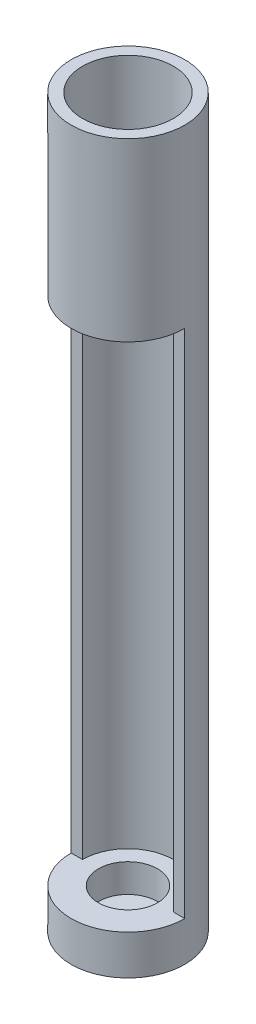
SolidWorks part; units mm, degrees
material "ABS PC"
ref_plane "Front Plane" through (0, 0, 0) normal (0, 0, 1) x (1, 0, 0)
ref_plane "Top Plane" through (0, 0, 0) normal (0, 1, 0) x (1, 0, 0)
ref_plane "Right Plane" through (0, 0, 0) normal (1, 0, 0) x (0, 0, -1)
sketch "Sketch1" plane through (0, 0, 0) normal (0, 1, 0) x (1, 0, 0)
  circle A0 centre (0, 0) radius 5
  dimension "D1" = 10
extrude "Boss-Extrude1" add sketch "Sketch1" along normal blind 3.5
sketch "Sketch2" plane through (0, 3.5, 0) normal (0, 1, 0) x (1, 0, 0)
  circle A0 centre (0, 0) radius 2.6
  dimension "D1" = 5.2
extrude "Cut-Extrude1" cut sketch "Sketch2" against normal blind 2.5
sketch "Sketch3" plane through (0, 3.5, 0) normal (0, 1, 0) x (1, 0, 0)
  line L0 (5, 0) -> (4, 0)
  line L1 (-5, 0) -> (-4, 0)
  arc A0 (5, 0) -> (-5, 0) centre (0, 0) ccw
  circle A1 centre (0, 0) radius 5 construction
  arc A2 (4, 0) -> (-4, 0) centre (0, 0) ccw
  circle M4 centre (0, 0) radius 5
  dimension "D1" = 1
  dimension "D2" = 1
extrude "Boss-Extrude2" add sketch "Sketch3" along normal blind 45 contours A2 L0 L1 M4
sketch "Sketch4" plane through (0, 48.5, 0) normal (0, 1, 0) x (1, 0, 0)
  circle A0 centre (0, 0) radius 5
  circle A2 centre (0, 0) radius 1.3
extrude "Boss-Extrude3" add sketch "Sketch4" along normal blind 3
ref_plane "Plane1" through (5, 3.5, 0) normal (-1, 0, 0) x (0, 0, 1)
sketch "Sketch7" plane through (0, 48.5, 0) normal (0, -1, 0) x (1, 0, 0)
  line L0 (0, 0) -> (0, 2.5) construction
  circle A0 centre (0, 2.5) radius 1
extrude "Cut-Extrude2" cut sketch "Sketch7" against normal blind 2
pattern_circular "CirPattern1" count 6 over 360 about axis through (0, 0, 0) along (0, 1, 0) of "Cut-Extrude2"
sketch "Sketch8" plane through (0, 51.5, 0) normal (0, 1, 0) x (1, 0, 0)
  circle A0 centre (0, 0) radius 5
  circle A3 centre (0, 0) radius 2.6
  dimension "D1" = 2.4
extrude "Boss-Extrude4" add sketch "Sketch8" along normal blind 2.5
sketch "Sketch9" plane through (0, 48.5, 0) normal (0, -1, 0) x (1, 0, 0)
  line L0 (0, 0) -> (0, 3) construction
  circle A0 centre (0, 3) radius 0.2
  dimension "D1" = 0.4
  dimension "D2" = 3
extrude "Cut-Extrude3" cut sketch "Sketch9" against normal through all
pattern_circular "CirPattern2" count 6 over 360 about axis through (0, 0, 0) along (0, 1, 0) of "Cut-Extrude3"
sketch "Sketch10" plane through (0, 54, 0) normal (0, 1, 0) x (1, 0, 0)
  circle A0 centre (0, 0) radius 5
  circle A1 centre (0, 0) radius 4
  dimension "D1" = 1
extrude "Boss-Extrude5" add sketch "Sketch10" along normal blind 10
